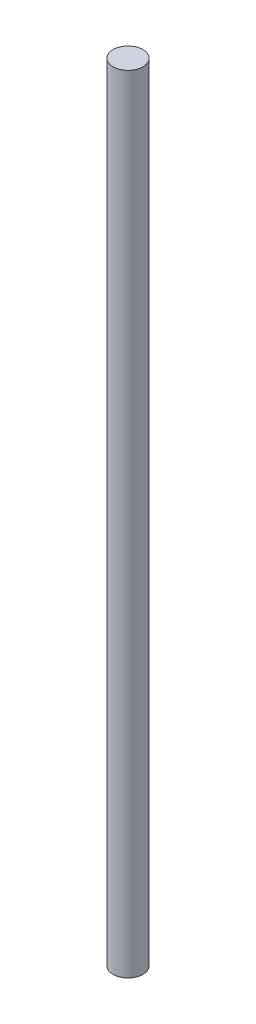
SolidWorks part; units mm, degrees
ref_plane "Front Plane" through (0, 0, 0) normal (0, 0, 1) x (1, 0, 0)
ref_plane "Top Plane" through (0, 0, 0) normal (0, 1, 0) x (1, 0, 0)
ref_plane "Right Plane" through (0, 0, 0) normal (1, 0, 0) x (0, 0, -1)
sketch "Sketch2" plane through (0, 0, 0) normal (0, 1, 0) x (1, 0, 0)
  circle A0 centre (0, 0) radius 0.75
  dimension "D1" = 1.5
extrude "Boss-Extrude1" add sketch "Sketch2" along normal blind 39.5
